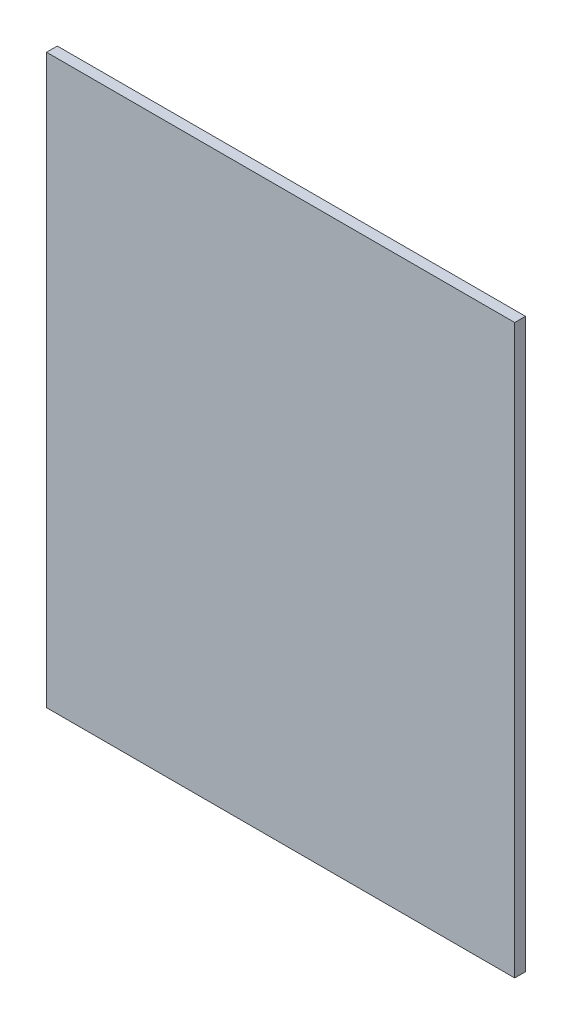
SolidWorks part; units mm, degrees
ref_plane "Front Plane" through (0, 0, 0) normal (0, 0, 1) x (1, 0, 0)
ref_plane "Top Plane" through (0, 0, 0) normal (0, 1, 0) x (1, 0, 0)
ref_plane "Right Plane" through (0, 0, 0) normal (1, 0, 0) x (0, 0, -1)
sketch "Sketch1" plane through (0, 0, 0) normal (0, 0, 1) x (1, 0, 0)
  line L1 (-129.267, -426.0852) -> (44.7972, -426.0852)
  line L2 (-129.267, -426.0852) -> (-129.267, -215.0378)
  line L3 (-129.267, -215.0378) -> (44.7972, -215.0378)
  line L4 (44.7972, -426.0852) -> (44.7972, -215.0378)
  line L6 (-129.267, -426.0852) -> (-129.267, -215.0378) construction
  line L8 (-114.9139, -409.7584) -> (-120.4139, -409.7584) construction
  line L9 (-119.735, -215.0378) -> (-114.9139, -215.0378) construction
extrude "Boss-Extrude1" add sketch "Sketch1" along normal blind 4
